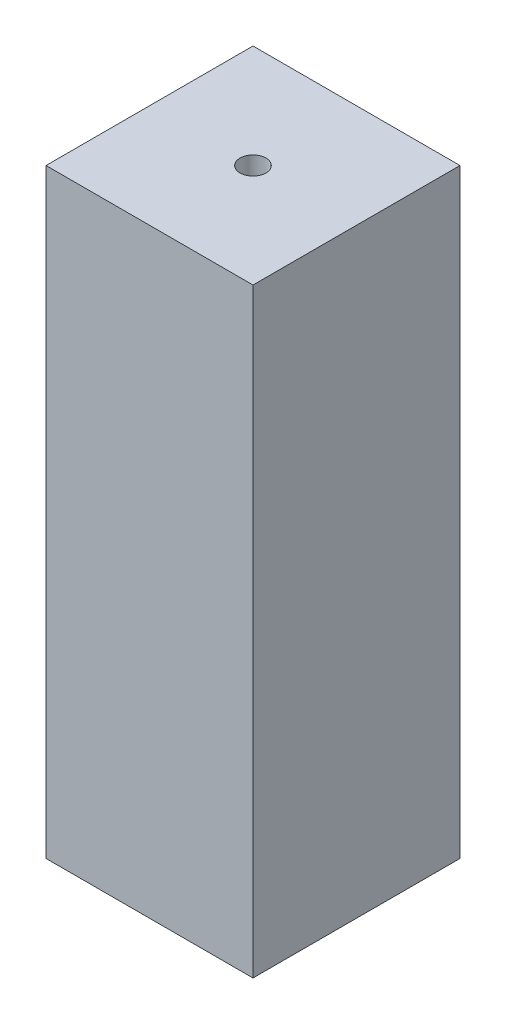
SolidWorks part; units mm, degrees
ref_plane "Front Plane" through (0, 0, 0) normal (0, 0, 1) x (1, 0, 0)
ref_plane "Top Plane" through (0, 0, 0) normal (0, 1, 0) x (1, 0, 0)
ref_plane "Right Plane" through (0, 0, 0) normal (1, 0, 0) x (0, 0, -1)
sketch "Sketch1" plane through (0, 0, 0) normal (0, 1, 0) x (1, 0, 0)
  line L1 (-12.7, -12.7) -> (12.7, -12.7)
  line L2 (-12.7, -12.7) -> (-12.7, 12.7)
  line L3 (-12.7, 12.7) -> (12.7, 12.7)
  line L4 (12.7, -12.7) -> (12.7, 12.7)
  line L5 (-12.7, -12.7) -> (12.7, 12.7) construction
  line L6 (-12.7, 12.7) -> (12.7, -12.7) construction
  point P0 (0, 0)
  dimension "D1" = 25.4
  dimension "D2" = 25.4
extrude "Boss-Extrude1" add sketch "Sketch1" along normal blind 73.65
sketch "Sketch2" plane through (0, 73.65, 0) normal (0, 1, 0) x (1, 0, 0)
  circle A1 centre (0, 0) radius 1.59
  dimension "D1" = 3.18
extrude "Cut-Extrude1" cut sketch "Sketch2" against normal blind 25.4
